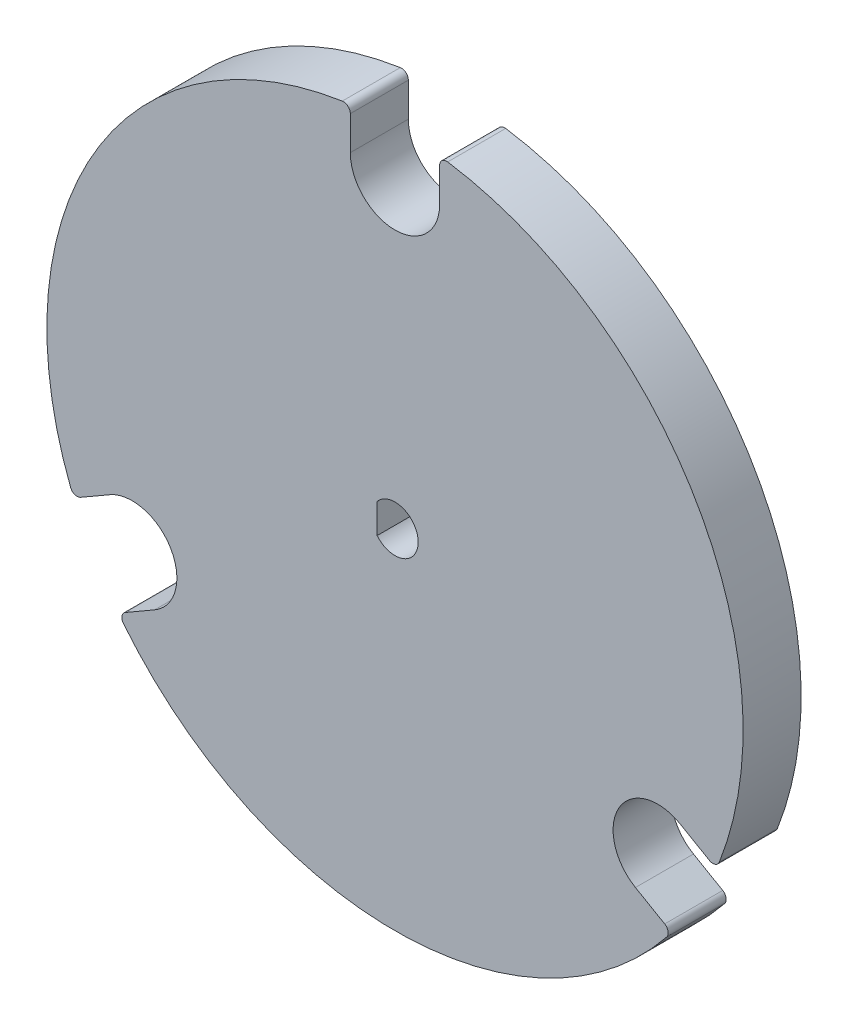
SolidWorks part; units mm, degrees
material "Acrylic (Medium-high impact)"
ref_plane "Front Plane" through (0, 0, 0) normal (0, 0, 1) x (1, 0, 0)
ref_plane "Top Plane" through (0, 0, 0) normal (0, 1, 0) x (1, 0, 0)
ref_plane "Right Plane" through (0, 0, 0) normal (1, 0, 0) x (0, 0, -1)
sketch "Sketch1" plane through (0, 0, 0) normal (0, 0, 1) x (1, 0, 0)
  circle A0 centre (0, 0) radius 38.1
  dimension "D1" = 76.2
extrude "Boss-Extrude1" add sketch "Sketch1" along normal blind 6.35
sketch "Sketch2" plane through (0, 0, 6.35) normal (0, 0, 1) x (1, 0, 0)
  line L0 (-4.8895, 33.2105) -> (-4.8895, 37.785)
  line L1 (0, 33.2105) -> (-28.7611, -16.6052) construction
  line L2 (-28.7611, -16.6052) -> (28.7611, -16.6052) construction
  line L3 (28.7611, -16.6052) -> (0, 33.2105) construction
  line L4 (4.8895, 33.2105) -> (4.8895, 37.785)
  line L5 (31.2059, -12.3708) -> (35.1675, -14.658)
  line L6 (26.3164, -20.8397) -> (30.278, -23.1269)
  line L7 (-26.3164, -20.8397) -> (-30.278, -23.1269)
  line L8 (-31.2059, -12.3708) -> (-35.1675, -14.658)
  circle A0 centre (0, 0) radius 16.6052 construction
  arc A1 (-4.8895, 33.2105) -> (4.8895, 33.2105) centre (0, 33.2105) ccw
  circle A2 centre (0, 0) radius 38.1 construction
  arc A3 (-4.8895, 37.785) -> (4.8895, 37.785) centre (0, 0) cw
  arc A4 (31.2059, -12.3708) -> (26.3164, -20.8397) centre (28.7611, -16.6052) ccw
  arc A5 (35.1675, -14.658) -> (30.278, -23.1269) centre (0, 0) cw
  arc A6 (-26.3164, -20.8397) -> (-31.2059, -12.3708) centre (-28.7611, -16.6053) ccw
  arc A7 (-30.278, -23.1269) -> (-35.1675, -14.658) centre (0, 0) cw
  point P25 (0, 0)
  dimension "D1" = 9.779
  dimension "D2" = 3
extrude "Cut-Extrude1" cut sketch "Sketch2" against normal through all
sketch "Sketch3" plane through (0, 0, 6.35) normal (0, 0, 1) x (1, 0, 0)
  line L2 (2.4934, -0.1813) -> (-1.4037, 2.0687)
  arc A1 (-1.4037, 2.0687) -> (2.4934, -0.1813) centre (0, 0) ccw
extrude "Cut-Extrude2" [suppressed] cut sketch "Sketch3" against normal through all
fillet "Fillet1" radius 0.762 6 edges at (-4.8895, 37.785, 3.175) (4.8895, 37.785, 3.175) (-30.278, -23.1269, 3.175) (-35.1675, -14.658, 3.175) (30.278, -23.1269, 3.175) (35.1675, -14.658, 3.175)
sketch "Sketch4" plane through (0, 0, 6.35) normal (0, 0, 1) x (1, 0, 0)
  line L0 (-1.9558, -1.6206) -> (-1.9558, 1.6206)
  line L1 (2.54, 3.6876) -> (2.54, -6.5459) construction
  arc A0 (-1.9558, -1.6206) -> (-1.9558, 1.6206) centre (0, 0) ccw
  dimension "D1" = 5.08
  dimension "D2" = 4.4958
extrude "Cut-Extrude3" cut sketch "Sketch4" against normal through all
